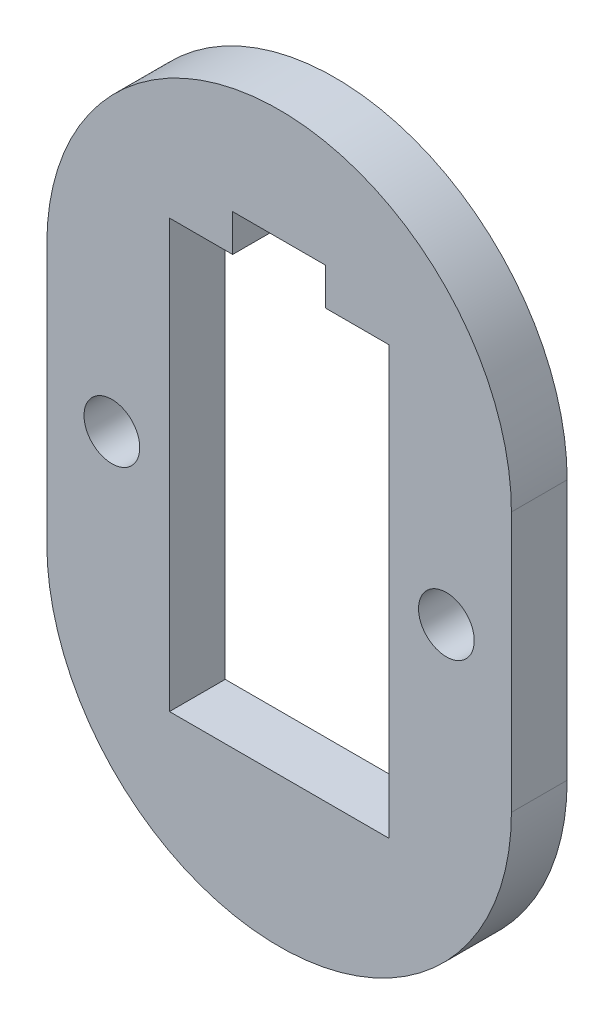
SolidWorks part; units mm, degrees
ref_plane "Front Plane" through (0, 0, 0) normal (0, 0, 1) x (1, 0, 0)
ref_plane "Top Plane" through (0, 0, 0) normal (0, 1, 0) x (1, 0, 0)
ref_plane "Right Plane" through (0, 0, 0) normal (1, 0, 0) x (0, 0, -1)
sketch "Model" plane through (0, 0, 0) normal (0, 0, 1) x (1, 0, 0)
  line L0 (54.5, 55.5001) -> (54.5, 53.5)
  line L1 (49.5, 53.5) -> (49.5, 55.5001)
  line L2 (49.5, 55.5001) -> (54.5, 55.5001)
  line L3 (54.5, 53.5) -> (57.9, 53.5)
  line L4 (46.1, 53.5) -> (49.5, 53.5)
  line L5 (46.1, 30.5) -> (57.9, 30.5)
  line L6 (64.5, 49) -> (64.5, 35)
  line L7 (46.1, 53.5) -> (46.1, 30.5)
  line L8 (57.9, 30.5) -> (57.9, 53.5)
  line L9 (39.5, 49.0001) -> (39.5, 35)
  circle A0 centre (43, 42) radius 1.5
  circle A1 centre (61, 42) radius 1.5
  arc A2 (64.5, 49) -> (39.5, 49.0001) centre (52, 49) ccw
  arc A3 (39.5, 35) -> (64.5, 35) centre (52, 35) ccw
extrude "Boss-Extrude1" add sketch "Model" along normal blind 3
